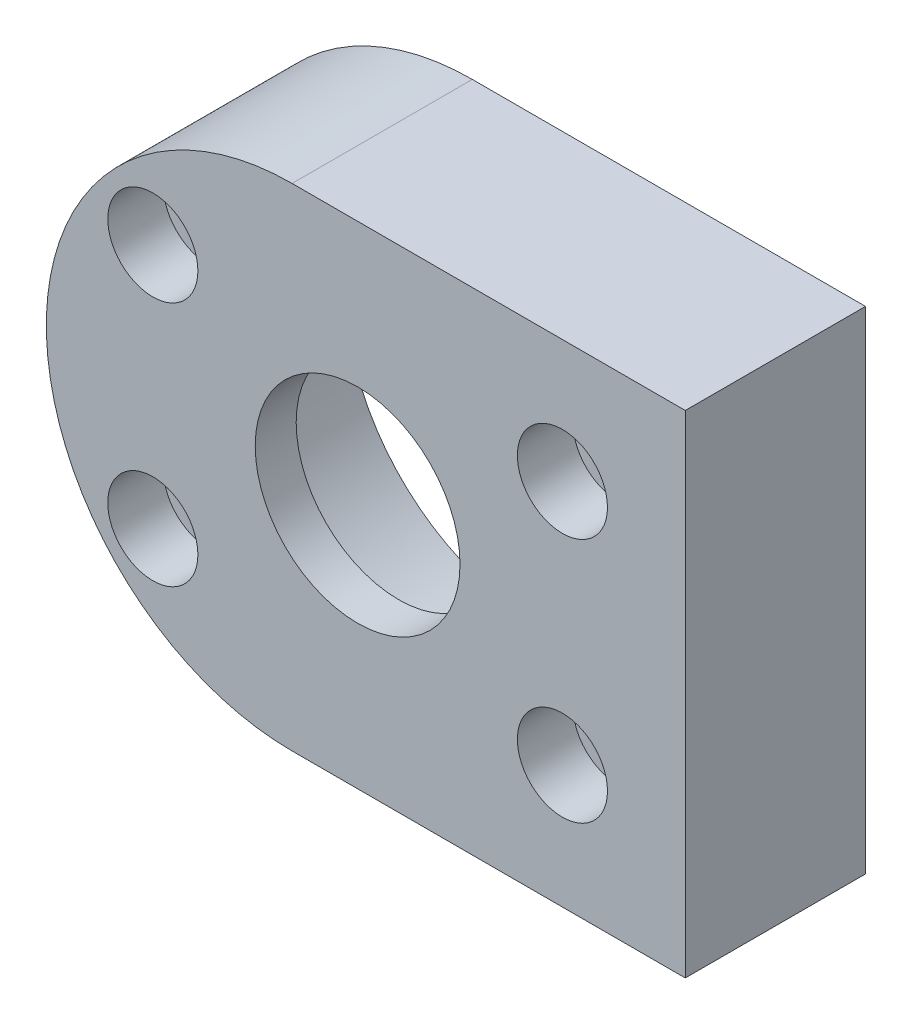
SolidWorks part; units mm, degrees
ref_plane "前视基准面" through (0, 0, 0) normal (0, 0, 1) x (1, 0, 0)
ref_plane "上视基准面" through (0, 0, 0) normal (0, 1, 0) x (1, 0, 0)
ref_plane "右视基准面" through (0, 0, 0) normal (1, 0, 0) x (0, 0, -1)
sketch "草图1" plane through (0, 0, 0) normal (0, 0, 1) x (1, 0, 0)
  line L0 (40, 0) -> (-120.2373, 0) construction
  line L1 (-8, 30) -> (40, 30)
  line L3 (-8, -30) -> (40, -30)
  line L4 (40, 30) -> (40, -30)
  arc A1 (-8, 30) -> (-8, -30) centre (-8, 0) ccw
  circle A2 centre (0, 0) radius 12.5
  point P0 (0, 0)
  dimension "D2" = 40
  dimension "D4" = 30
  dimension "D5" = 25
  dimension "D1" = 60
  dimension "D3" = 48
extrude "凸台-拉伸1" add sketch "草图1" along normal blind 22
sketch "草图3" plane through (0, 0, 22) normal (0, 0, 1) x (1, 0, 0)
  line L1 (-25, 15) -> (25, 15)
  line L2 (-25, 15) -> (-25, -15)
  line L3 (-25, -15) -> (25, -15)
  line L4 (25, 15) -> (25, -15)
  line L5 (-25, 15) -> (25, -15) construction
  line L6 (-25, -15) -> (25, 15) construction
  point P0 (0, 0)
  dimension "D1" = 30
  dimension "D2" = 50
hole_wizard "打孔尺寸(%根据)内六角圆柱头螺钉的类型1" positions "3D草图1" profile "草图4" counterbore size "M6" standard "GB" end condition through all
sketch3d "3D草图1"
  point P0 (-25, 15, 22)
  point P3 (-25, -15, 22)
  point P6 (25, 15, 22)
  point P9 (25, -15, 22)
sketch "草图4" plane through (-25, 15, 22) normal (1, 0, 0) x (0, -1, 0)
  line L0 (0, 0) -> (0, 22)
  line L1 (0, 22) -> (3.3, 22)
  line L3 (3.3, 22) -> (3.3, 6.8)
  line L4 (3.3, 6.8) -> (5.5, 6.8)
  line L5 (5.5, 6.8) -> (5.5, 0)
  line L7 (5.5, 0) -> (0, 0)
  line L11 (0, -6.35) -> (0, 107.95) construction
  dimension "通孔孔直径" = 6.6
  dimension "通孔孔深度" = 22
  dimension "柱形沉头孔直径" = 11
  dimension "柱形沉头孔深度" = 6.8
sketch "草图5" plane through (0, 0, 0) normal (0, 0, -1) x (-1, 0, 0)
  circle A0 centre (0, 0) radius 23.5
  dimension "D1" = 47
extrude "切除-拉伸1" cut sketch "草图5" against normal blind 13
sketch "草图6" plane through (0, 0, 13) normal (0, 0, -1) x (-1, 0, 0)
  circle A0 centre (0, 0) radius 20
  dimension "D1" = 40
extrude "切除-拉伸2" cut sketch "草图6" against normal blind 4
